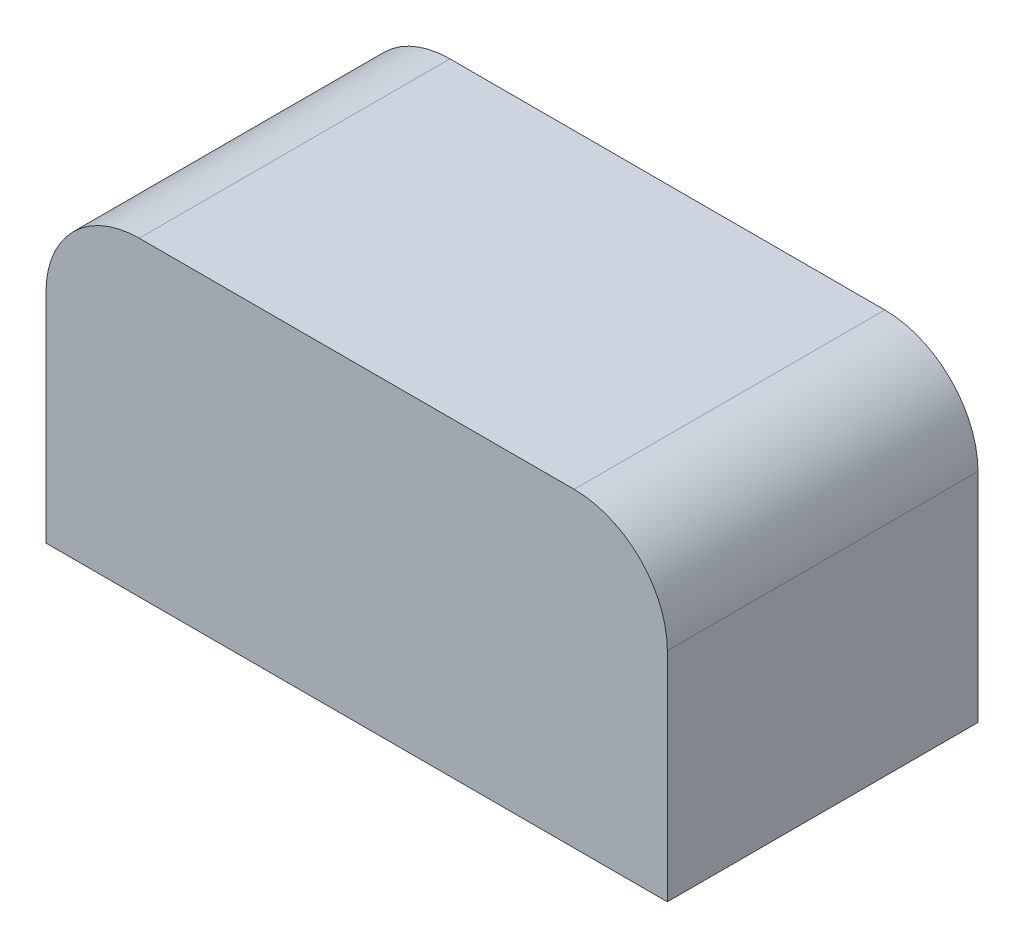
SolidWorks part; units mm, degrees
ref_plane "Front Plane" through (0, 0, 0) normal (0, 0, 1) x (1, 0, 0)
ref_plane "Top Plane" through (0, 0, 0) normal (0, 1, 0) x (1, 0, 0)
ref_plane "Right Plane" through (0, 0, 0) normal (1, 0, 0) x (0, 0, -1)
sketch "Sketch1" plane through (0, 0, 0) normal (0, 0, 1) x (1, 0, 0)
  line L0 (-165.3614, 249.3811) -> (-159.1604, 249.3811) construction
  line L1 (-173.0217, 239.3811) -> (-153.0217, 239.3811)
  line L2 (-173.0217, 239.3811) -> (-173.0217, 249.3811)
  line L3 (-173.0217, 249.3811) -> (-153.0217, 249.3811)
  line L4 (-153.0217, 239.3811) -> (-153.0217, 249.3811)
  dimension "D1" = 10
  dimension "D2" = 0
  dimension "D3" = 20
extrude "Boss-Extrude1" add sketch "Sketch1" along normal blind 10
fillet "Fillet1" radius 3
